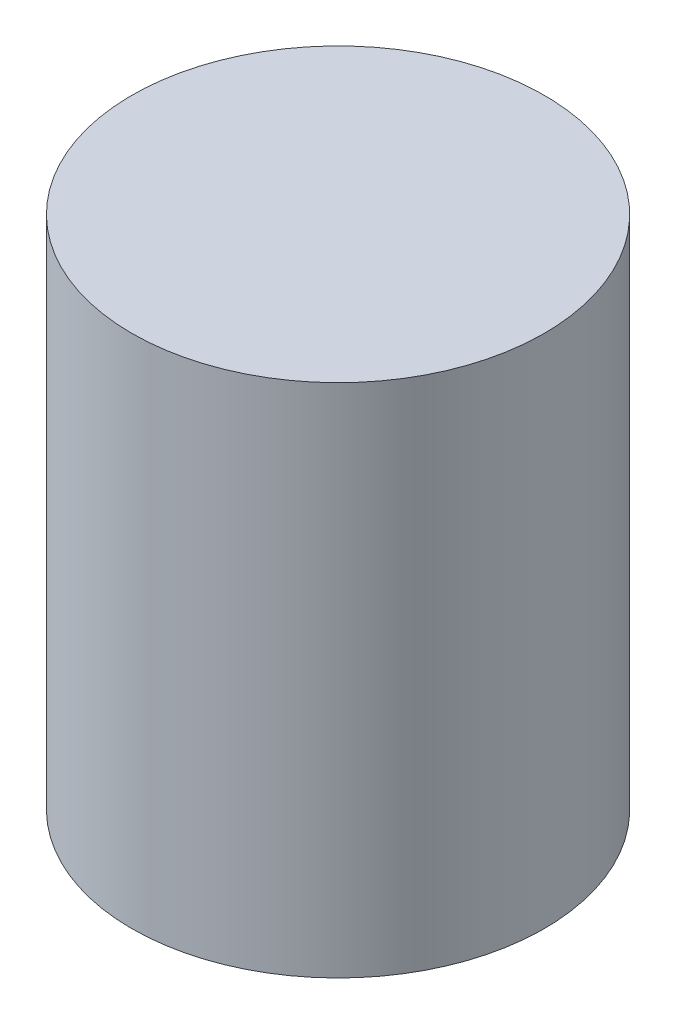
SolidWorks part; units mm, degrees
ref_plane "前视基准面" through (0, 0, 0) normal (0, 0, 1) x (1, 0, 0)
ref_plane "上视基准面" through (0, 0, 0) normal (0, 1, 0) x (1, 0, 0)
ref_plane "右视基准面" through (0, 0, 0) normal (1, 0, 0) x (0, 0, -1)
sketch "草图1" plane through (0, 0, 0) normal (0, 1, 0) x (1, 0, 0)
  circle A0 centre (0, 0) radius 8
  dimension "D1" = 16
extrude "凸台-拉伸1" add sketch "草图1" along normal blind 20
